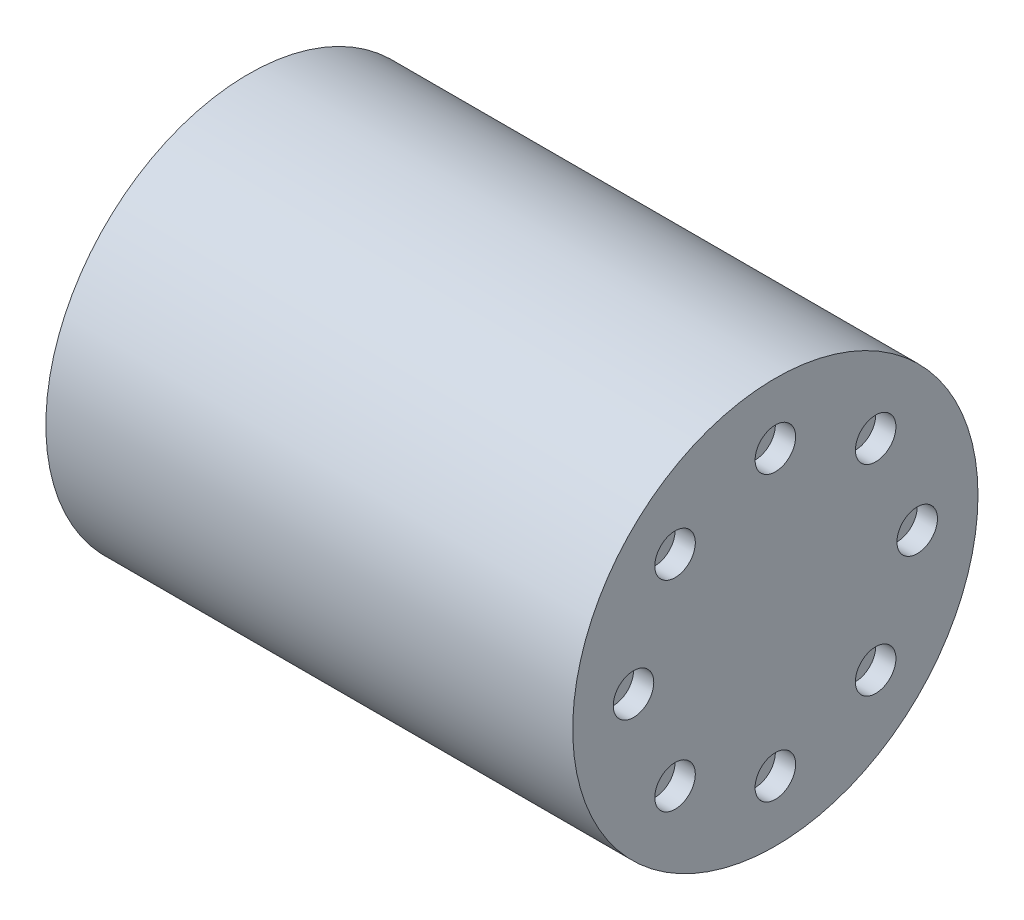
SolidWorks part; units mm, degrees
ref_plane "Front Plane" through (0, 0, 0) normal (0, 0, 1) x (1, 0, 0)
ref_plane "Top Plane" through (0, 0, 0) normal (0, 1, 0) x (1, 0, 0)
ref_plane "Right Plane" through (0, 0, 0) normal (1, 0, 0) x (0, 0, -1)
sketch "Sketch1" plane through (0, 0, 0) normal (1, 0, 0) x (0, 0, -1)
  circle A0 centre (0, 0) radius 50
  dimension "D1" = 100
extrude "Boss-Extrude1" add sketch "Sketch1" along normal mid plane 130
sketch "Sketch2" plane through (-65, 0, 0) normal (-1, 0, 0) x (0, 0, 1)
  circle A0 centre (0, 0) radius 4
  dimension "D1" = 8
extrude "Boss-Extrude2" add sketch "Sketch2" along normal blind 12
sketch "Sketch3" plane through (-65, 0, 0) normal (-1, 0, 0) x (0, 0, 1)
  circle A0 centre (0, 35) radius 5
  dimension "D2" = 10
  dimension "D1" = 35
extrude "Cut-Extrude1" cut sketch "Sketch3" against normal blind 5
pattern_circular "CirPattern1" count 8 over 360 about axis through (0, 0, 0) along (1, 0, 0) of "Cut-Extrude1"
sketch "Sketch4" plane through (65, 0, 0) normal (1, 0, 0) x (0, 0, -1)
  circle A0 centre (0, 35) radius 5
  dimension "D1" = 10
  dimension "D2" = 35
extrude "Cut-Extrude2" cut sketch "Sketch4" against normal blind 5
pattern_circular "CirPattern2" count 8 over 360 about axis through (0, 0, 0) along (1, 0, 0) of "Cut-Extrude2"
